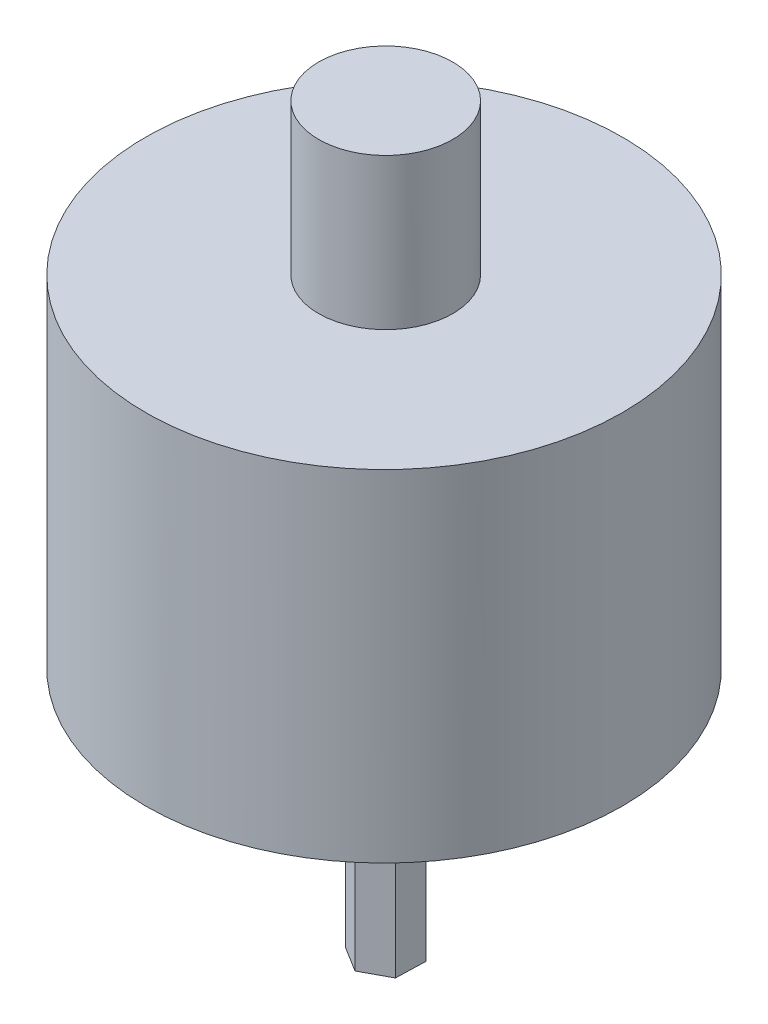
SolidWorks part; units mm, degrees
ref_plane "Front Plane" through (0, 0, 0) normal (0, 0, 1) x (1, 0, 0)
ref_plane "Top Plane" through (0, 0, 0) normal (0, 1, 0) x (1, 0, 0)
ref_plane "Right Plane" through (0, 0, 0) normal (1, 0, 0) x (0, 0, -1)
sketch "Sketch1" plane through (0, 0, 0) normal (0, 1, 0) x (1, 0, 0)
  line L19 (17.0349, -13.1371) -> (17.9145, -12.6638)
  line L20 (17.9145, -12.6638) -> (17.9444, -11.6654)
  line L21 (17.9444, -11.6654) -> (17.0947, -11.1403)
  line L22 (17.0947, -11.1403) -> (16.2152, -11.6136)
  line L23 (16.2152, -11.6136) -> (16.1853, -12.612)
  line L24 (16.1853, -12.612) -> (17.0349, -13.1371)
  circle A0 centre (17.0648, -12.1387) radius 0.865 construction
  point P1 (-0.1084, -1.1793)
extrude "Boss-Extrude1" add sketch "Sketch1" along normal up to surface (8.305 mm away)
sketch "Sketch2" plane through (0, 8.305, 0) normal (0, 1, 0) x (1, 0, 0)
  line L0 (17.9145, -12.6638) -> (17.9444, -11.6654) construction
  circle A0 centre (17.0349, -12.1646) radius 8
  point P2 (0, -2.1776)
  point P3 (0, 0)
  point P4 (-0.1485, -2.2035)
  point P6 (0, 0)
  point P9 (17.9294, -12.1646)
  dimension "D1" = 16
extrude "Boss-Extrude2" add sketch "Sketch2" along normal up to surface (11.43 mm away)
sketch "Sketch3" plane through (0, 19.735, 0) normal (0, 1, 0) x (1, 0, 0)
  circle A0 centre (17.0648, -12.1387) radius 2.25
  point P2 (0, 0)
  point P3 (-0.1383, -2.1776)
  dimension "D1" = 4.5
extrude "Boss-Extrude3" add sketch "Sketch3" along normal up to surface (5.06 mm away)
